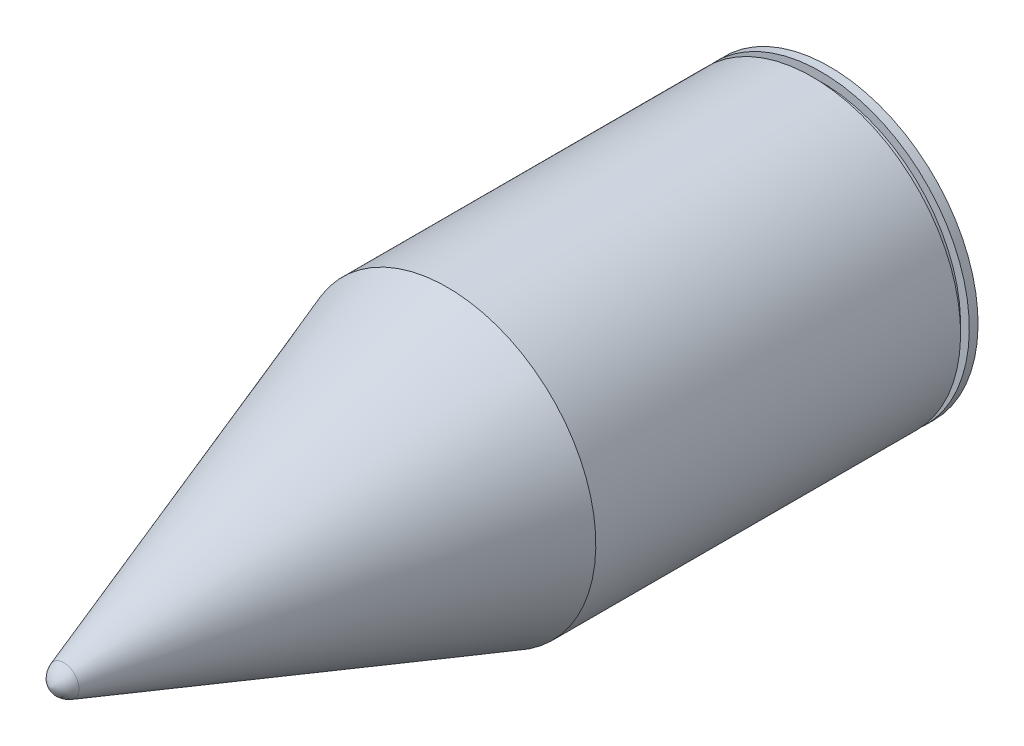
SolidWorks part; units mm, degrees
ref_plane "Front Plane" through (0, 0, 0) normal (0, 0, 1) x (1, 0, 0)
ref_plane "Top Plane" through (0, 0, 0) normal (0, 1, 0) x (1, 0, 0)
ref_plane "Right Plane" through (0, 0, 0) normal (1, 0, 0) x (0, 0, -1)
sketch "Sketch1" plane through (0, 0, 0) normal (1, 0, 0) x (0, 0, -1)
  line L0 (297.4164, 1.2365) -> (1504.0831, 1.2365) construction
  line L1 (0, 0) -> (1790.1723, -11.1346) construction
  line L2 (428.0276, -2.6623) -> (1790.1723, -11.1346) construction
  line L3 (428.0276, -2.6623) -> (428.0276, 89.9825) construction
  line L4 (428.0276, 89.9825) -> (227.5599, 89.9825)
  line L5 (227.5599, 89.9825) -> (42.9885, 25.8263)
  line L6 (474.2833, 187.5427) -> (35.5474, 35.04)
  line L7 (0, 23.0914) -> (3731.1003, -0.1154) construction
  line L8 (892.1008, 17.5427) -> (892.1008, 187.5427) construction
  line L9 (892.1008, 17.5427) -> (3731.1003, -0.1154) construction
  line L10 (892.1008, 187.5427) -> (474.2833, 187.5427)
  arc A0 (42.9885, 25.8263) -> (13.6132, 15.6083) centre (23317.3768, -66932.4053) ccw
  arc A1 (13.6132, 15.6083) -> (0, 0) centre (20.4813, -4.1226) ccw
  arc A2 (56.9839, -26.6307) -> (0, 23.0914) centre (42.6874, 14.499) ccw
  arc A3 (35.5474, 35.04) -> (56.9839, -26.6307) centre (46.2657, 4.2047) ccw
  dimension "D1" = 1362.1446
  dimension "D2" = 92.6447
  dimension "D3" = 170
sketch "Sketch2" plane through (0, 0, 0) normal (1, 0, 0) x (0, 0, -1)
  line L0 (0, 0) -> (902, 0) construction
  line L1 (872, 170) -> (872, 160)
  line L2 (872, 160) -> (882, 160)
  line L3 (882, 160) -> (882, 170)
  line L4 (882, 170) -> (892, 170)
  line L5 (454.1825, 170) -> (14.8069, 17.275)
  line L6 (892, 170) -> (892, 155)
  line L7 (872, 0) -> (872, 170) construction
  line L8 (892, 155) -> (902, 155)
  line L9 (872, 170) -> (454.1825, 170)
  line L10 (902, 155) -> (902, 0)
  line L11 (0, 0) -> (902, 0)
  arc A0 (14.8069, 17.275) -> (0, 0) centre (22.2252, -4.0667) ccw
  dimension "D1" = 15
  dimension "D2" = 902
  dimension "D3" = 170
revolve "Revolve1" add sketch "Sketch2" angle 360 about L11
